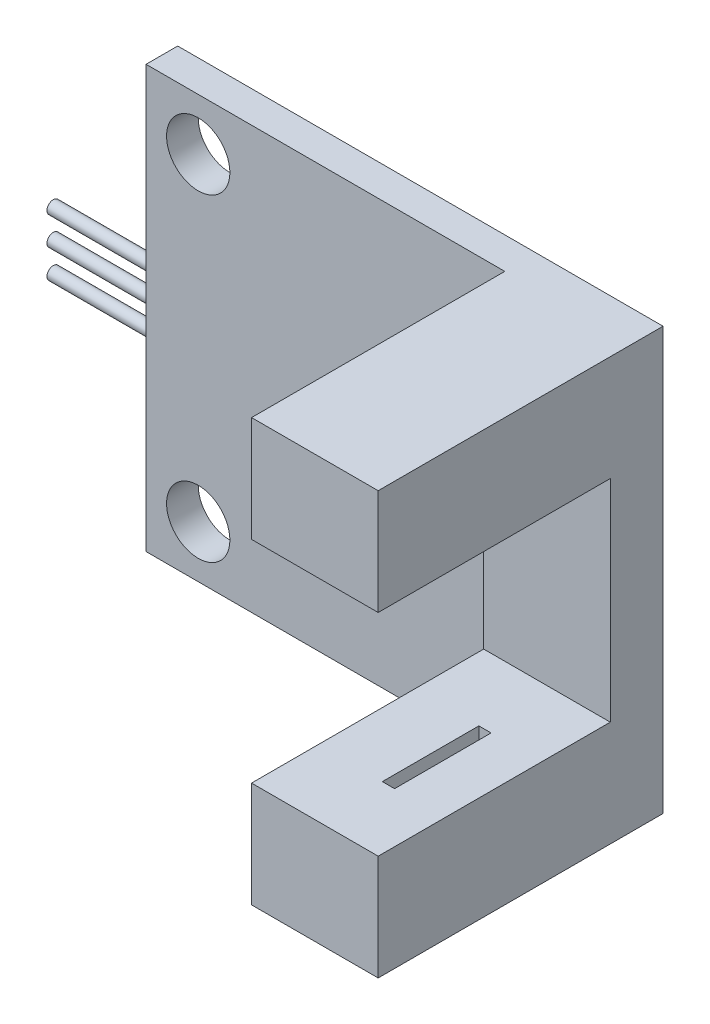
SolidWorks part; units mm, degrees
ref_plane "前视基准面" through (0, 0, 0) normal (0, 0, 1) x (1, 0, 0)
ref_plane "上视基准面" through (0, 0, 0) normal (0, 1, 0) x (1, 0, 0)
ref_plane "右视基准面" through (0, 0, 0) normal (1, 0, 0) x (0, 0, -1)
sketch "草图1" plane through (0, 0, 0) normal (0, 0, 1) x (1, 0, 0)
  line L1 (-11.5, -10) -> (11.5, -10)
  line L2 (-11.5, -10) -> (-11.5, 10)
  line L3 (-11.5, 10) -> (11.5, 10)
  line L4 (11.5, -10) -> (11.5, 10)
  line L5 (-11.5, -10) -> (11.5, 10) construction
  line L6 (-11.5, 10) -> (11.5, -10) construction
  point P0 (0, 0)
  dimension "D1" = 23
  dimension "D2" = 20
extrude "凸台-拉伸1" add sketch "草图1" along normal blind 1.5
sketch "草图2" plane through (0, 0, 1.5) normal (0, 0, 1) x (1, 0, 0)
  line L0 (-11.5, -10) -> (11.5, -10) construction
  line L1 (11.5, -10) -> (11.5, 10) construction
  line L2 (11.5, 10) -> (-11.5, 10) construction
  line L3 (5.5, -10) -> (11.5, -10)
  line L4 (11.5, -10) -> (11.5, 10)
  line L5 (11.5, 10) -> (5.5, 10)
  line L6 (5.5, 10) -> (5.5, -10)
  dimension "D1" = 6
extrude "凸台-拉伸2" add sketch "草图2" along normal blind 12
sketch "草图3" plane through (0, 0, 13.5) normal (0, 0, 1) x (1, 0, 0)
  line L0 (11.5, -10) -> (11.5, 10) construction
  line L1 (5.5, -5) -> (11.5, -5)
  line L2 (5.5, -5) -> (5.5, 5)
  line L3 (5.5, 5) -> (11.5, 5)
  line L4 (11.5, -5) -> (11.5, 5)
  line L5 (5.5, -5) -> (11.5, 5) construction
  line L6 (5.5, 5) -> (11.5, -5) construction
  line L7 (5.5, 10) -> (5.5, -10) construction
  point P0 (8.5, 0)
  point P9 (0, 0)
  point P10 (0, 0)
  dimension "D1" = 10
extrude "切除-拉伸1" cut sketch "草图3" against normal blind 11
sketch "草图4" plane through (-11.5, 0, 0) normal (-1, 0, 0) x (0, 0, 1)
  circle A0 centre (0.8967, 1.3435) radius 0.3
  circle A1 centre (0.8967, 0) radius 0.3
  circle A2 centre (0.8967, -1.3612) radius 0.3
  point P6 (0, 0)
  point P7 (0.9775, 1.9893)
  point P8 (1.1296, 0.9136)
  point P9 (0.8598, -1.3612)
  point P10 (0.8882, 0)
  point P11 (0.8967, 1.3435)
  dimension "D1" = 0.6
extrude "凸台-拉伸3" add sketch "草图4" along normal blind 5
sketch "草图5" plane through (0, 0, 1.5) normal (0, 0, 1) x (1, 0, 0)
  circle A0 centre (-9.0282, -7.5406) radius 1.5
  point P2 (-9.2463, -7.7332)
  point P3 (-9.0282, -7.5406)
  point P4 (0, 0)
  dimension "D1" = 3
extrude "切除-拉伸2" cut sketch "草图5" against normal blind 7
mirror "镜向1" about plane through (0, 0, 0) normal (0, 1, 0) of "切除-拉伸2"
sketch "草图6" plane through (0, -5, 0) normal (0, 1, 0) x (1, 0, 0)
  line L1 (8.539, -10.3413) -> (9.1186, -10.3413)
  line L2 (8.539, -10.3413) -> (8.539, -5.7681)
  line L3 (8.539, -5.7681) -> (9.1186, -5.7681)
  line L4 (9.1186, -10.3413) -> (9.1186, -5.7681)
  line L5 (8.539, -10.3413) -> (9.1186, -5.7681) construction
  line L6 (8.539, -5.7681) -> (9.1186, -10.3413) construction
  point P0 (8.8288, -8.0547)
extrude "切除-拉伸3" cut sketch "草图6" against normal blind 2
mirror "镜向2" about plane through (0, 0, 0) normal (0, 1, 0) of "切除-拉伸3"
